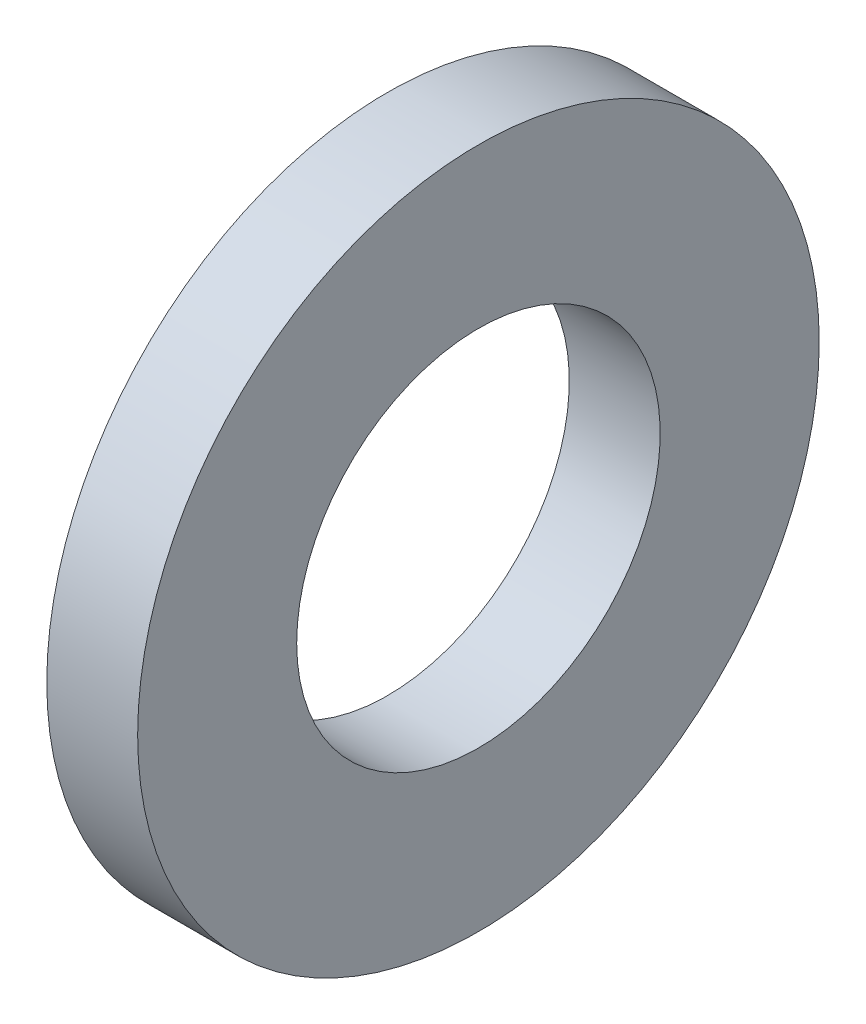
SolidWorks part; units mm, degrees
ref_plane "Plane1" through (0, 0, 0) normal (0, 0, 1) x (1, 0, 0)
ref_plane "Plane2" through (0, 0, 0) normal (0, 1, 0) x (1, 0, 0)
ref_plane "Plane3" through (0, 0, 0) normal (1, 0, 0) x (0, 0, -1)
revolve "Base-Revolve" add sketch "Sketch1" angle 360 about L0
sketch "Sketch1" plane through (0, 0, 0) normal (0, 0, 1) x (1, 0, 0)
  line L0 (-34.925, 0) -> (9.525, 0) construction
  line L1 (0, 3.2) -> (0, 6)
  line L2 (0, 6) -> (-1.6, 6)
  line L3 (-1.6, 6) -> (-1.6, 3.2)
  line L4 (-1.6, 3.2) -> (0, 3.2)
  dimension "Thickness" = 1.6
  dimension "Inside_dia" = 6.4
  dimension "Outside_dia" = 12
